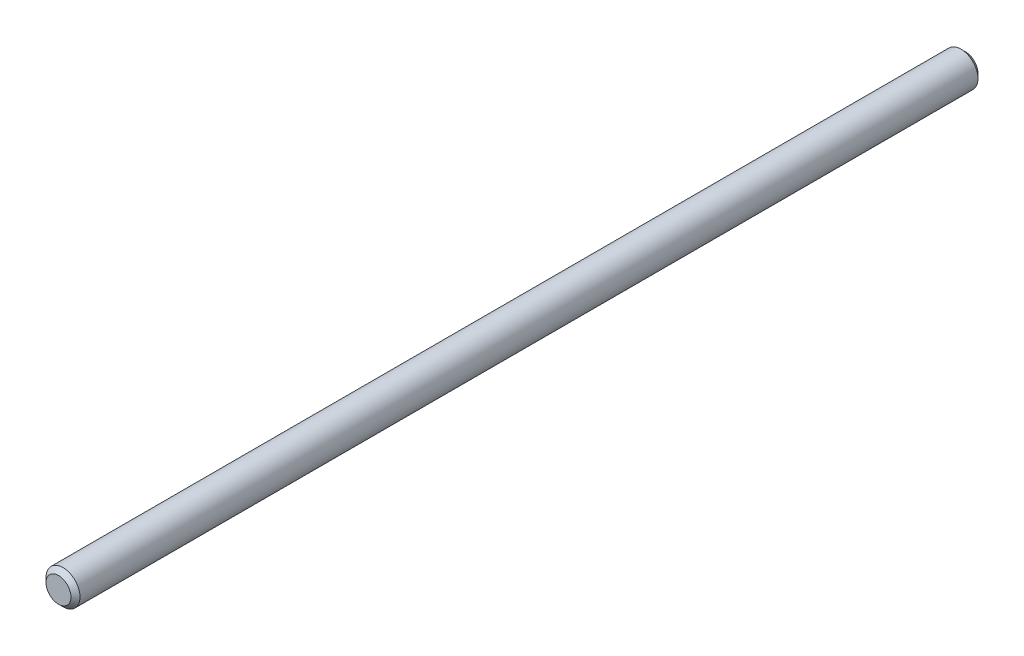
SolidWorks part; units mm, degrees
ref_plane "Alzado" through (0, 0, 0) normal (0, 0, 1) x (1, 0, 0)
ref_plane "Planta" through (0, 0, 0) normal (0, 1, 0) x (1, 0, 0)
ref_plane "Vista lateral" through (0, 0, 0) normal (1, 0, 0) x (0, 0, -1)
sketch "Croquis1" plane through (0, 0, 0) normal (0, 0, 1) x (1, 0, 0)
  circle A0 centre (0, 0) radius 7.5
  dimension "D1" = 15
extrude "Saliente-Extruir1" add sketch "Croquis1" along normal blind 400
chamfer "Chaflán1" distance 2 angle 45 2 edges at (7.5, 0, 400) (7.5, 0, 0)
